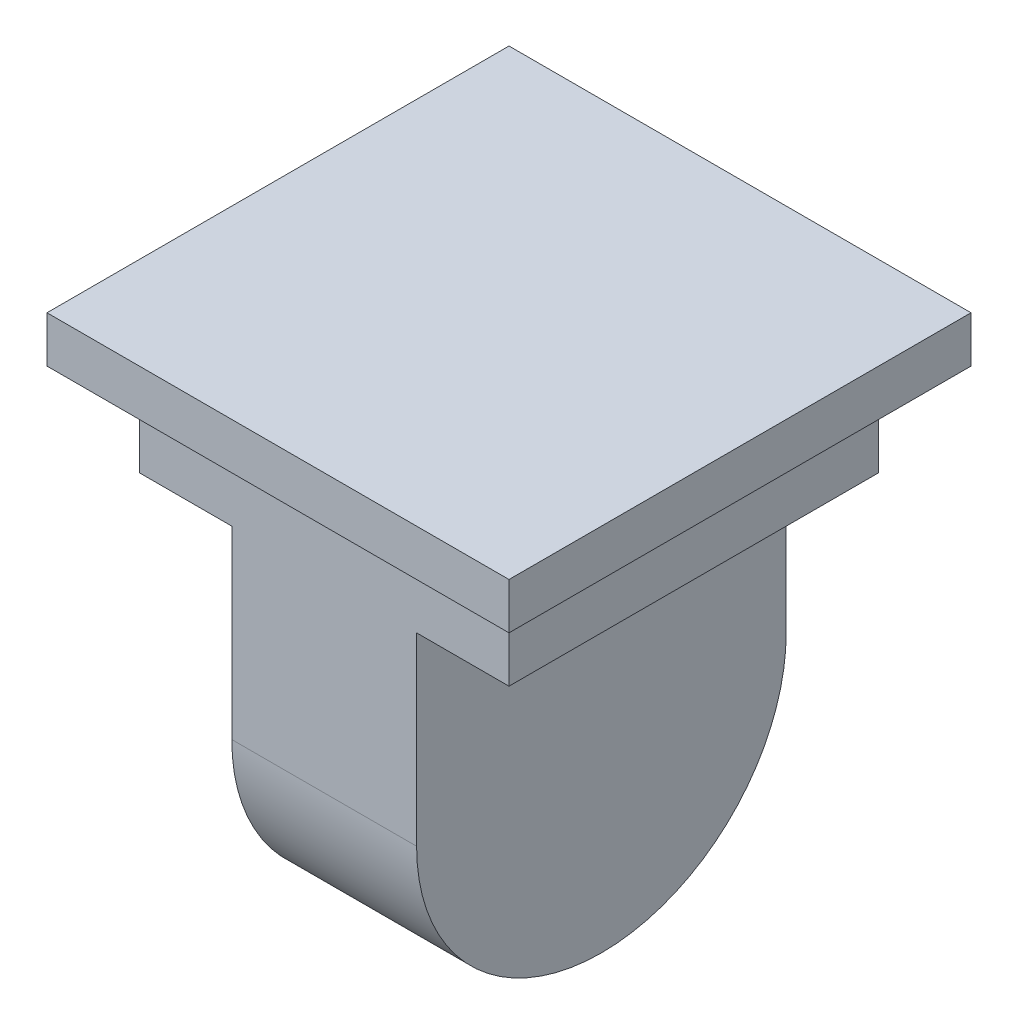
SolidWorks part; units mm, degrees
ref_plane "Front" through (0, 0, 0) normal (0, 0, 1) x (1, 0, 0)
ref_plane "Top" through (0, 0, 0) normal (0, 1, 0) x (1, 0, 0)
ref_plane "Right" through (0, 0, 0) normal (1, 0, 0) x (0, 0, -1)
sketch "草图1" plane through (0, 0, 0) normal (0, 1, 0) x (1, 0, 0)
  line L0 (-18.2439, 0) -> (0, 0) construction
  line L1 (0, 0) -> (0, 18.5122) construction
  line L3 (-8, 8) -> (8, 8)
  line L4 (-8, 8) -> (-8, -8)
  line L5 (-8, -8) -> (8, -8)
  line L6 (8, 8) -> (8, -8)
  dimension "D1" = 16
  dimension "D2" = 16
  dimension "D3" = 8
  dimension "D4" = 8
extrude "凸台-拉伸1" add sketch "草图1" along normal blind 20
sketch "草图2" plane through (8, 0, 0) normal (1, 0, 0) x (0, 0, -1)
  line L0 (0, 0) -> (0, 20) construction
  line L1 (-8, 20) -> (8, 20) construction
  line L4 (-8, 8) -> (-8, -6.7486)
  line L5 (-8, -6.7486) -> (8, -6.7486)
  line L6 (8, 8) -> (8, -6.7486)
  arc A0 (-8, 8) -> (8, 8) centre (0, 8) ccw
extrude "切除-拉伸1" cut sketch "草图2" against normal blind 40
sketch "草图4" plane through (-8, 0, 0) normal (-1, 0, 0) x (0, 0, 1)
  line L0 (8, 20) -> (8, 8) construction
  line L2 (-8, 8) -> (-8, 16)
  line L3 (-8, 16) -> (8, 16)
  line L4 (8, 8) -> (8, 16)
  arc A0 (-8, 8) -> (8, 8) centre (0, 8) ccw
extrude "切除-拉伸2" cut sketch "草图4" against normal blind 4
sketch "草图5" plane through (8, 0, 0) normal (1, 0, 0) x (0, 0, -1)
  line L0 (0, 0) -> (0, 20) construction
  line L1 (-8, 20) -> (8, 20) construction
  line L4 (-8, 8) -> (-8, 16)
  line L5 (-8, 16) -> (8, 16)
  line L6 (8, 8) -> (8, 16)
  arc A0 (-8, 8) -> (8, 8) centre (0, 8) ccw
extrude "切除-拉伸3" cut sketch "草图5" against normal blind 4
sketch "草图6" plane through (0, 20, 0) normal (0, 1, 0) x (1, 0, 0)
  line L1 (-10, 10) -> (10, 10)
  line L2 (-10, 10) -> (-10, -10)
  line L3 (-10, -10) -> (10, -10)
  line L4 (10, 10) -> (10, -10)
  dimension "D1" = 20
  dimension "D2" = 20
  dimension "D3" = 10
  dimension "D4" = 10
extrude "凸台-拉伸2" add sketch "草图6" along normal blind 2
